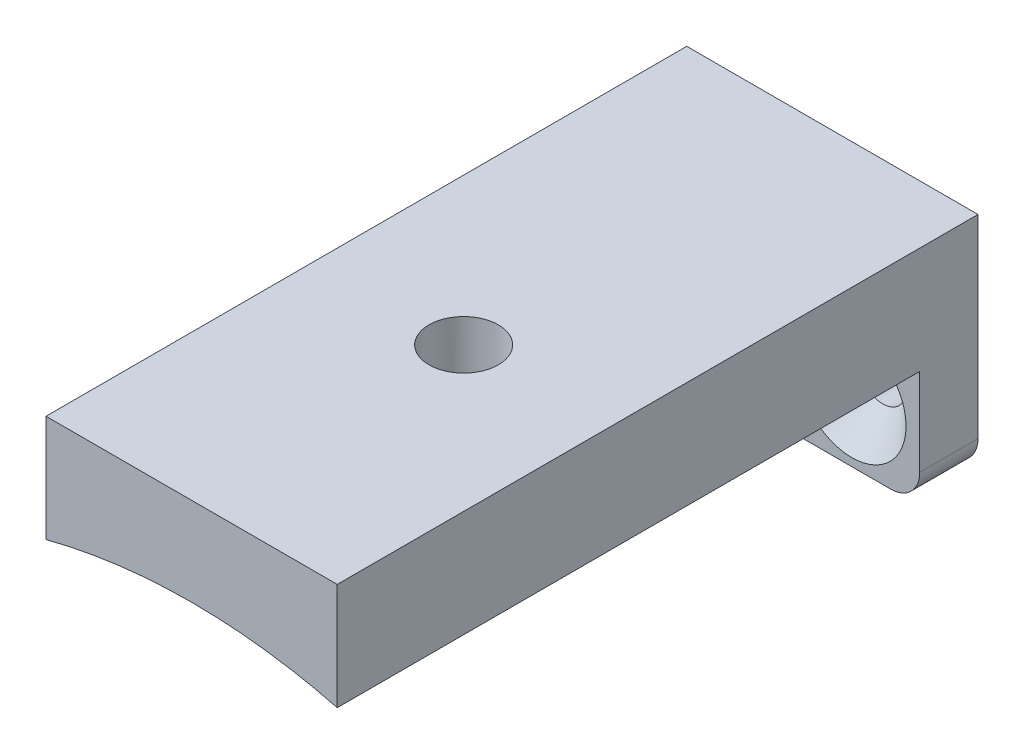
SolidWorks part; units mm, degrees
ref_plane "Ebene vorne" through (0, 0, 0) normal (0, 0, 1) x (1, 0, 0)
ref_plane "Ebene oben" through (0, 0, 0) normal (0, 1, 0) x (1, 0, 0)
ref_plane "Ebene rechts" through (0, 0, 0) normal (1, 0, 0) x (0, 0, -1)
sketch "Skizze1" plane through (0, 0, 0) normal (0, 0, 1) x (1, 0, 0)
  line L0 (-15, 12) -> (-15, 3)
  line L1 (-12, 0) -> (12, 0)
  line L2 (15, 3) -> (15, 12)
  arc A0 (-15, 12) -> (15, 12) centre (0, -46.0948) cw
  arc A1 (12, 0) -> (15, 3) centre (12, 3) ccw
  arc A2 (-15, 3) -> (-12, 0) centre (-12, 3) ccw
  point P3 (0, 13.9052)
  point P10 (15, 0)
  point P13 (-15, 0)
  dimension "D1" = 60
  dimension "D4" = 3
  dimension "D2" = 12
  dimension "D3" = 30
extrude "Aufsatz-Linear austragen1" add sketch "Skizze1" along normal blind 6
hole_wizard "Formsenkung für M4 Senkschraube mit Innensechskant1" positions "Skizze2" profile "Skizze3" countersink size "M4" standard "DIN" end condition through all
sketch "Skizze2" plane through (0, 0, 6) normal (0, 0, 1) x (1, 0, 0)
  line L0 (0, 0) -> (0, 13.9052) construction
  line L2 (-15, 12) -> (-15, 3) construction
  line L3 (-12, 0) -> (12, 0) construction
  arc A0 (15, 12) -> (-15, 12) centre (0, -46.0948) ccw construction
  point P0 (-8, 6.4)
  point P12 (8, 6.4)
  dimension "D1" = 7
  dimension "D2" = 6.4
sketch "Skizze3" plane through (-8, 6.4, 6) normal (1, 0, 0) x (0, -1, 0)
  line L0 (0, 0) -> (0, 6)
  line L1 (0, 6) -> (2.4, 6)
  line L2 (2.4, 6) -> (2.4, 3.19)
  line L3 (2.4, 3.19) -> (5.59, 0)
  line L5 (5.59, 0) -> (0, 0)
  line L6 (-2.4, 3.19) -> (-5.59, 0) construction
  line L11 (0, -6.35) -> (0, 107.95) construction
  dimension "Bohrerdurchmesser" = 4.8
  dimension "Bohrungstiefe" = 6
  dimension "Senkdurchmesser (Oben)" = 11.18
  dimension "Senkwinkel (Oben)" = 90
sketch "Skizze4" plane through (0, 0, 6) normal (0, 0, 1) x (1, 0, 0)
  line L0 (-15, 12) -> (-15, 23)
  line L1 (-15, 23) -> (15, 23)
  line L2 (15, 23) -> (15, 12)
  arc A0 (15, 12) -> (-15, 12) centre (0, -46.0948) ccw construction
  arc A1 (15, 12) -> (-15, 12) centre (0, -46.0948) ccw
  dimension "D1" = 11
extrude "Aufsatz-Linear austragen2" add sketch "Skizze4" along normal blind 60 and the other way up to vertex (6 mm away) contours L0 L1 L2 A1 other way up to point (-15, 12, 0)
hole_wizard "Stirnsenkung für 1/4 Flachkopfschraube (Kopf Button)1" positions "3D-Skizze1" profile "Skizze5" counterbore size "1/4" standard "ANSI Inch" end condition through all
sketch3d "3D-Skizze1"
  line L0 (15, 12, 6) -> (15, 12, 66) construction
  line L1 (-12, 0, 6) -> (12, 0, 6) construction
  point P0 (0.1215, 13.9051, 38.1193)
  dimension "D1" = 15
  dimension "D2" = 35
sketch "Skizze5" plane through (0.1215, 13.9051, 38.1193) normal (0, 0, 1) x (1, -0.002, 0)
  line L0 (0, 0) -> (0, 9.125)
  line L1 (0, 9.125) -> (3.5712, 9.125)
  line L3 (3.5712, 9.125) -> (3.5712, 0.5)
  line L4 (3.5712, 0.5) -> (5.9538, 0.5)
  line L5 (5.9538, 0.5) -> (5.9538, 0)
  line L7 (5.9538, 0) -> (0, 0)
  line L11 (0, -6.35) -> (0, 107.95) construction
  dimension "Bohrerdurchmesser" = 7.1425
  dimension "Bohrungstiefe" = 9.125
  dimension "Senkdurchmesser2" = 11.9075
  dimension "Senktiefe2" = 0.5
